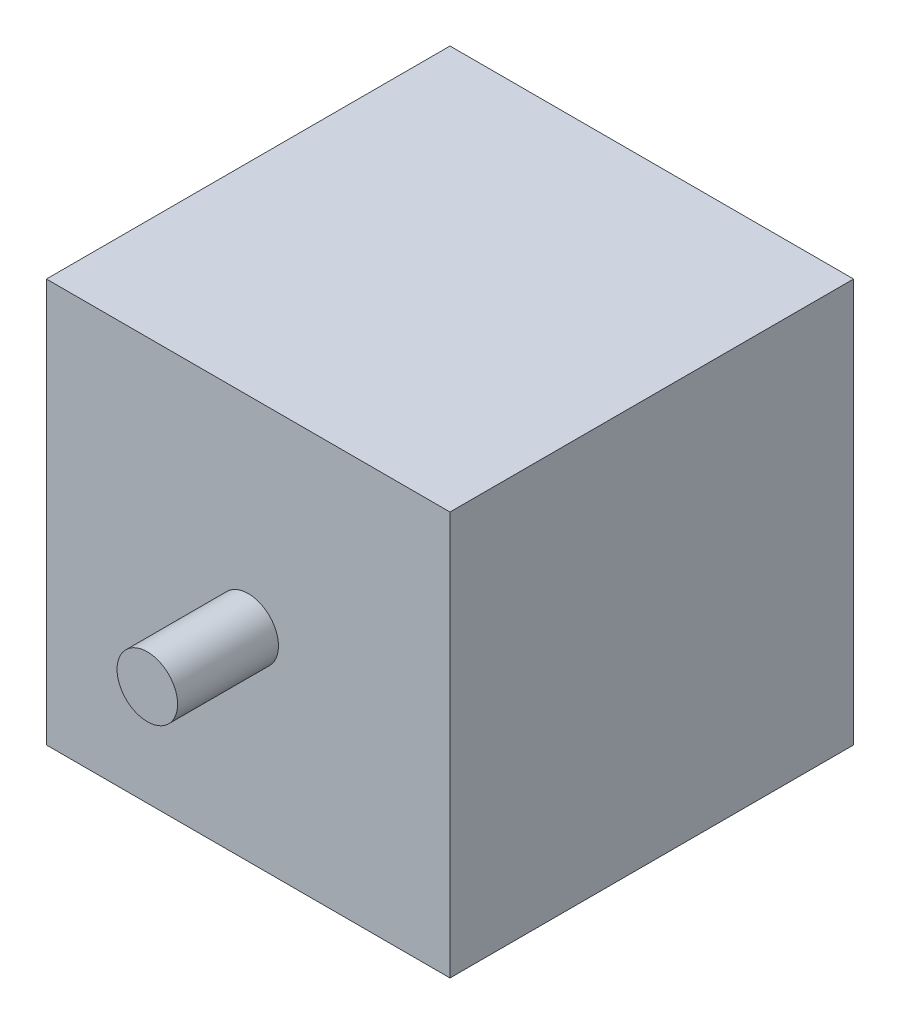
SolidWorks part; units mm, degrees
ref_plane "Front Plane" through (0, 0, 0) normal (0, 0, 1) x (1, 0, 0)
ref_plane "Top Plane" through (0, 0, 0) normal (0, 1, 0) x (1, 0, 0)
ref_plane "Right Plane" through (0, 0, 0) normal (1, 0, 0) x (0, 0, -1)
sketch "Sketch1" plane through (0, 0, 0) normal (0, 0, 1) x (1, 0, 0)
  line L1 (-20, -20) -> (20, -20)
  line L2 (-20, -20) -> (-20, 20)
  line L3 (-20, 20) -> (20, 20)
  line L4 (20, -20) -> (20, 20)
  line L5 (-20, -20) -> (20, 20) construction
  line L6 (-20, 20) -> (20, -20) construction
  point P0 (0, 0)
extrude "Boss-Extrude1" add sketch "Sketch1" along normal blind 40
sketch "Sketch2" plane through (0, 0, 40) normal (0, 0, 1) x (1, 0, 0)
  circle A0 centre (0, 0) radius 3
extrude "Boss-Extrude2" add sketch "Sketch2" along normal blind 10
